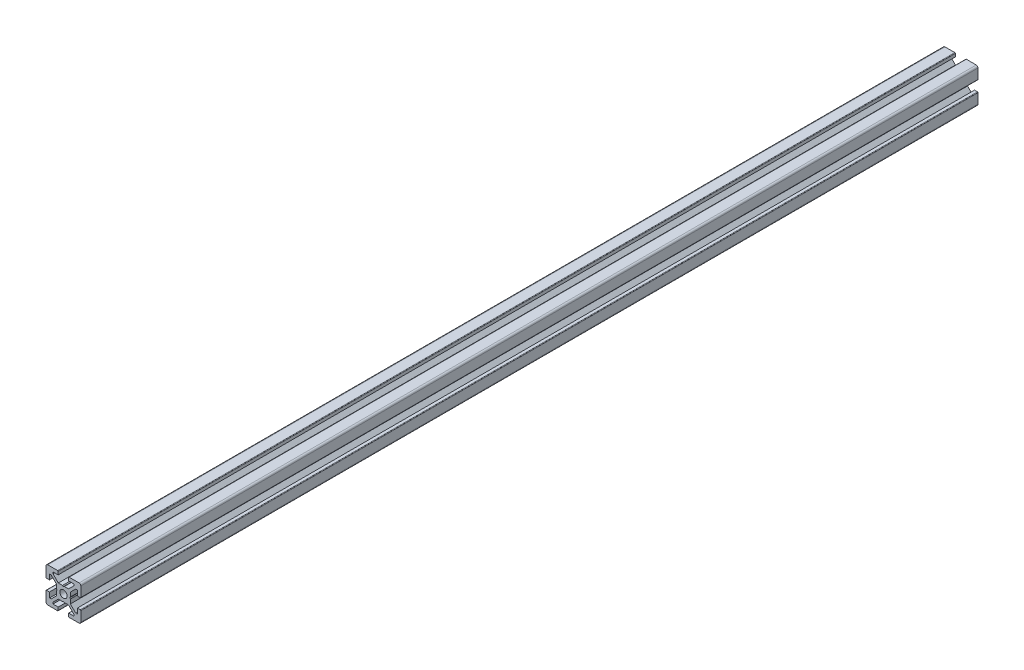
SolidWorks part; units mm, degrees
material "6063-T5"
ref_plane "Front Plane" through (0, 0, 0) normal (0, 0, 1) x (1, 0, 0)
ref_plane "Top Plane" through (0, 0, 0) normal (0, 1, 0) x (1, 0, 0)
ref_plane "Right Plane" through (0, 0, 0) normal (1, 0, 0) x (0, 0, -1)
ref_plane "Plane1" through (0, 0, 0) normal (0, 0, 1) x (1, 0, 0)
sketch "Sketch1" plane through (0, 0, 0) normal (0, 0, 1) x (1, 0, 0)
  line L0 (-10, 9) -> (-10, 3.3)
  line L1 (-9.7, 3) -> (-8, 3)
  line L2 (-8, 3) -> (-8, 6)
  line L3 (-8, 6) -> (-7.0607, 6)
  line L4 (-7.0607, 6) -> (-4, 2.9393)
  line L5 (-4, 2.9393) -> (-4, 0.5196)
  line L6 (-4, 0.5196) -> (-3.7, 0)
  line L7 (-3.7, 0) -> (-4, -0.5196)
  line L8 (-4, -0.5196) -> (-4, -2.9393)
  line L9 (-4, -2.9393) -> (-7.0607, -6)
  line L10 (-7.0607, -6) -> (-8, -6)
  line L11 (-8, -6) -> (-8, -3)
  line L12 (-8, -3) -> (-9.7, -3)
  line L13 (-10, -3.3) -> (-10, -9)
  line L14 (-9, -10) -> (-3.3, -10)
  line L15 (-3, -9.7) -> (-3, -8)
  line L16 (-3, -8) -> (-6, -8)
  line L17 (-6, -8) -> (-6, -7.0607)
  line L18 (-6, -7.0607) -> (-2.9393, -4)
  line L19 (-2.9393, -4) -> (-0.5196, -4)
  line L20 (-0.5196, -4) -> (0, -3.7)
  line L21 (0, -3.7) -> (0.5196, -4)
  line L22 (0.5196, -4) -> (2.9393, -4)
  line L23 (2.9393, -4) -> (6, -7.0607)
  line L24 (6, -7.0607) -> (6, -8)
  line L25 (6, -8) -> (3, -8)
  line L26 (3, -8) -> (3, -9.7)
  line L27 (3.3, -10) -> (9, -10)
  line L28 (10, -9) -> (10, -3.3)
  line L29 (9.7, -3) -> (8, -3)
  line L30 (8, -3) -> (8, -6)
  line L31 (8, -6) -> (7.0606, -6)
  line L32 (7.0606, -6) -> (4, -2.9393)
  line L33 (4, -2.9393) -> (4, -0.5196)
  line L34 (4, -0.5196) -> (3.7, 0)
  line L35 (3.7, 0) -> (4, 0.5196)
  line L36 (4, 0.5196) -> (4, 2.9393)
  line L37 (4, 2.9393) -> (7.0607, 6)
  line L38 (7.0607, 6) -> (8, 6)
  line L39 (8, 6) -> (8, 3)
  line L40 (8, 3) -> (9.7, 3)
  line L41 (10, 3.3) -> (10, 9)
  line L42 (9, 10) -> (3.3, 10)
  line L43 (3, 9.7) -> (3, 8)
  line L44 (3, 8) -> (6, 8)
  line L45 (6, 8) -> (6, 7.0607)
  line L46 (6, 7.0607) -> (2.9393, 4)
  line L47 (2.9393, 4) -> (0.5196, 4)
  line L48 (0.5196, 4) -> (0, 3.7)
  line L49 (0, 3.7) -> (-0.5196, 4)
  line L50 (-0.5196, 4) -> (-2.9394, 4)
  line L51 (-2.9394, 4) -> (-6, 7.0606)
  line L52 (-6, 7.0606) -> (-6, 8)
  line L53 (-6, 8) -> (-3, 8)
  line L54 (-3, 8) -> (-3, 9.7)
  line L55 (-3.3, 10) -> (-9, 10)
  arc A0 (-10, 3.3) -> (-9.7, 3) centre (-9.7, 3.3) ccw
  arc A1 (-9.7, -3) -> (-10, -3.3) centre (-9.7, -3.3) ccw
  arc A2 (-10, -9) -> (-9, -10) centre (-9, -9) ccw
  arc A3 (-3.3, -10) -> (-3, -9.7) centre (-3.3, -9.7) ccw
  arc A4 (3, -9.7) -> (3.3, -10) centre (3.3, -9.7) ccw
  arc A5 (9, -10) -> (10, -9) centre (9, -9) ccw
  arc A6 (10, -3.3) -> (9.7, -3) centre (9.7, -3.3) ccw
  arc A7 (9.7, 3) -> (10, 3.3) centre (9.7, 3.3) ccw
  arc A8 (10, 9) -> (9, 10) centre (9, 9) ccw
  arc A9 (3.3, 10) -> (3, 9.7) centre (3.3, 9.7) ccw
  arc A10 (-3, 9.7) -> (-3.3, 10) centre (-3.3, 9.7) ccw
  arc A11 (-9, 10) -> (-10, 9) centre (-9, 9) ccw
extrude "Boss-Extrude1" add sketch "Sketch1" against normal blind 515
ref_plane "Plane2" through (0, 0, 0) normal (1, 0, 0) x (0, 0, -1)
sketch "Sketch2" plane through (0, 0, 0) normal (1, 0, 0) x (0, 0, -1)
  line L0 (0, 0) -> (0, 2.1)
  line L1 (0, 2.1) -> (515, 2.1)
  line L2 (515, 2.1) -> (515, 0)
  line L3 (515, 0) -> (0, 0)
  line L4 (515, 0) -> (0, 0) construction
  dimension "D1" = 2.1
  dimension "D2" = 515
revolve "Cut-Revolve1" cut sketch "Sketch2" angle 360 about L4
ref_plane "Plane3" through (0, 0, -257.5) normal (0, 0, 1) x (1, 0, 0)
